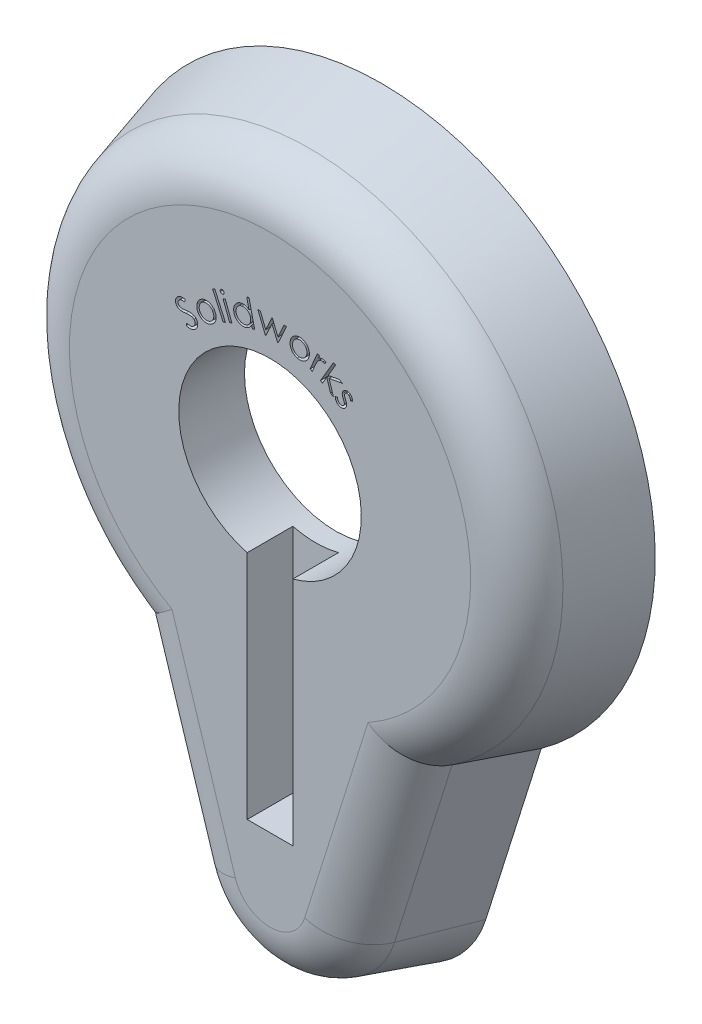
SolidWorks part; units mm, degrees
ref_plane "Front Plane" through (0, 0, 0) normal (0, 0, 1) x (1, 0, 0)
ref_plane "Top Plane" through (0, 0, 0) normal (0, 1, 0) x (1, 0, 0)
ref_plane "Right Plane" through (0, 0, 0) normal (1, 0, 0) x (0, 0, -1)
sketch "Sketch1" plane through (0, 0, 0) normal (0, 0, 1) x (1, 0, 0)
  line L0 (0, 69.8088) -> (0, -73.1976) construction
  line L1 (-22.2438, -18.7082) -> (-14.5346, -43.1583)
  line L2 (22.2438, -18.7082) -> (14.5346, -43.1583)
  arc A0 (-14.5346, -43.1583) -> (14.5346, -43.1583) centre (0, -38.5756) ccw
  arc A1 (-22.2438, -18.7082) -> (22.2438, -18.7082) centre (0, 12.2244) cw
  dimension "D1" = 38.1
  dimension "D3" = 15.24
  dimension "D4" = 50.8
  dimension "D2" = 35
extrude "Boss-Extrude1" add sketch "Sketch1" along normal blind 15.494 draft 16
fillet "Fillet2" radius 7.62 4 edges at (-14.3818, -28.8685, 15.494) (14.3818, -28.8685, 15.494) (0, -49.3727, 15.494) (0, 45.8816, 15.494)
sketch "Sketch2" plane through (0, 0, 0) normal (0, 0, -1) x (-1, 0, 0)
  line L4 (-20.0801, -17.1235) -> (-12.1122, -42.3945)
  line L5 (12.1122, -42.3945) -> (20.0801, -17.1235)
  line L6 (-20.0801, -17.1235) -> (-12.1122, -42.3945)
  line L7 (12.1122, -42.3945) -> (20.0801, -17.1235)
  arc A4 (20.0801, -17.1235) -> (-20.0801, -17.1235) centre (0, 12.2244) ccw
  arc A5 (-12.1122, -42.3945) -> (12.1122, -42.3945) centre (0, -38.5756) ccw
  arc A6 (20.0801, -17.1235) -> (-20.0801, -17.1235) centre (0, 12.2244) ccw
  arc A7 (-12.1122, -42.3945) -> (12.1122, -42.3945) centre (0, -38.5756) ccw
  dimension "D1" = 2.54
extrude "Cut-Extrude1" cut sketch "Sketch2" against normal blind 6.35
sketch "Sketch3" plane through (0, 0, 15.494) normal (0, 0, 1) x (1, 0, 0)
  circle A0 centre (0, 12.2244) radius 12.7
  dimension "D1" = 25.4
extrude "Cut-Extrude3" cut sketch "Sketch3" against normal blind 21.336
sketch "Sketch5" plane through (0, 0, 15.494) normal (0, 0, 1) x (1, 0, 0)
  line L0 (0, -32.2256) -> (0, -38.5756) construction
  line L1 (-3.175, 18.5744) -> (3.175, 18.5744)
  line L2 (-3.175, 18.5744) -> (-3.175, -32.2256)
  line L3 (-3.175, -32.2256) -> (3.175, -32.2256)
  line L4 (3.175, 18.5744) -> (3.175, -32.2256)
  point P6 (63.5424, -26.1141)
  point P7 (61.6648, -18.8069)
  point P8 (0, -38.5756)
  dimension "D1" = 6.35
  dimension "D2" = 6.35
  dimension "D3" = 50.8
sketch "Sketch6" plane through (0, 0, 15.494) normal (0, 0, 1) x (1, 0, 0)
extrude "Cut-Extrude11" cut sketch "Sketch5" against normal blind 6.35
sketch "Sketch7" plane through (0, 0, 15.494) normal (0, 0, 1) x (1, 0, 0)
  arc A0 (-11.2648, 22.534) -> (10.3095, 23.4893) centre (0, 12.2244) cw construction
  text T0 "Solidworks"
extrude "Cut-Extrude12" cut sketch "Sketch7" against normal blind 6.35
